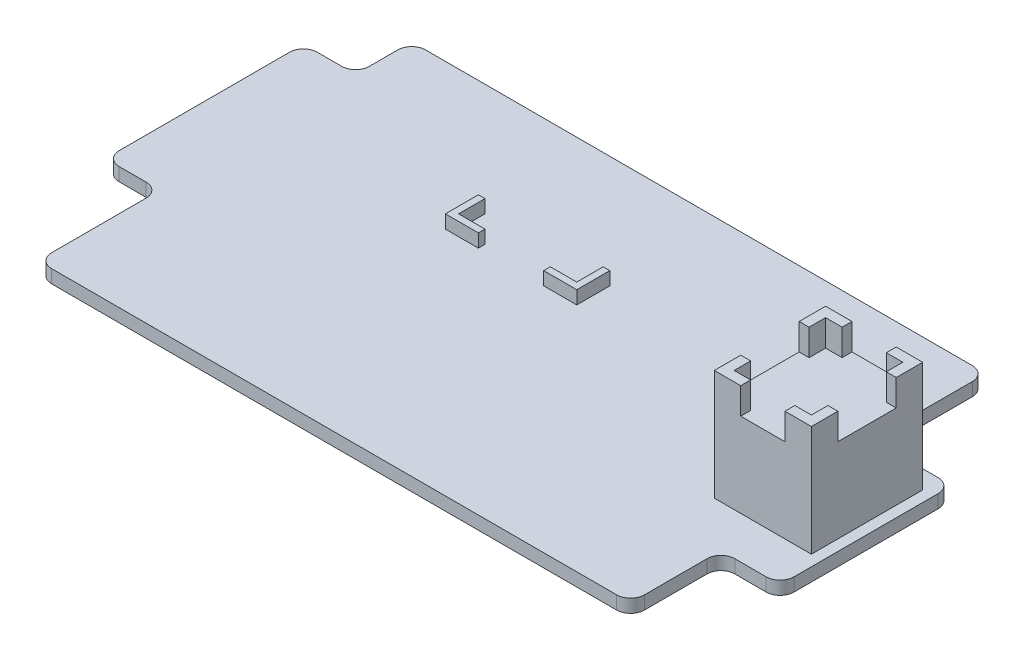
SolidWorks part; units mm, degrees
ref_plane "Front Plane" through (0, 0, 0) normal (0, 0, 1) x (1, 0, 0)
ref_plane "Top Plane" through (0, 0, 0) normal (0, 1, 0) x (1, 0, 0)
ref_plane "Right Plane" through (0, 0, 0) normal (1, 0, 0) x (0, 0, -1)
sketch "Sketch1" plane through (0, 0, 0) normal (0, 1, 0) x (1, 0, 0)
  line L36 (-14.34, 86.924) -> (-97.14, 86.924)
  line L37 (-12.24, 71.7409) -> (-12.24, 84.824)
  line L38 (-2.2334, 69.6409) -> (-10.14, 69.6409)
  line L39 (-0.1334, 45.7095) -> (-0.1334, 67.5409)
  line L40 (-6.9951, 43.6095) -> (-2.2334, 43.6095)
  line L41 (-9.0951, 32.024) -> (-9.0951, 41.5095)
  line L42 (-96.7563, 29.924) -> (-11.1951, 29.924)
  line L43 (-98.8563, 46.3225) -> (-98.8563, 32.024)
  line L44 (-105.0334, 48.4225) -> (-100.9563, 48.4225)
  line L45 (-107.1334, 76.3225) -> (-107.1334, 50.5225)
  line L46 (-101.34, 78.4225) -> (-105.0334, 78.4225)
  line L47 (-99.24, 84.824) -> (-99.24, 80.5225)
  arc A36 (-12.24, 84.824) -> (-14.34, 86.924) centre (-14.34, 84.824) ccw
  arc A37 (-12.24, 71.7409) -> (-10.14, 69.6409) centre (-10.14, 71.7409) ccw
  arc A38 (-0.1334, 67.5409) -> (-2.2334, 69.6409) centre (-2.2334, 67.5409) ccw
  arc A39 (-2.2334, 43.6095) -> (-0.1334, 45.7095) centre (-2.2334, 45.7095) ccw
  arc A40 (-6.9951, 43.6095) -> (-9.0951, 41.5095) centre (-6.9951, 41.5095) ccw
  arc A41 (-11.1951, 29.924) -> (-9.0951, 32.024) centre (-11.1951, 32.024) ccw
  arc A42 (-98.8563, 32.024) -> (-96.7563, 29.924) centre (-96.7563, 32.024) ccw
  arc A43 (-98.8563, 46.3225) -> (-100.9563, 48.4225) centre (-100.9563, 46.3225) ccw
  arc A44 (-107.1334, 50.5225) -> (-105.0334, 48.4225) centre (-105.0334, 50.5225) ccw
  arc A45 (-105.0334, 78.4225) -> (-107.1334, 76.3225) centre (-105.0334, 76.3225) ccw
  arc A46 (-101.34, 78.4225) -> (-99.24, 80.5225) centre (-101.34, 80.5225) ccw
  arc A47 (-97.14, 86.924) -> (-99.24, 84.824) centre (-97.14, 84.824) ccw
extrude "Boss-Extrude1" add sketch "Sketch1" along normal blind 2
sketch "Sketch2" plane through (0, 2, 0) normal (0, 1, 0) x (1, 0, 0)
  line L1 (-52.24, 64.924) -> (-57.24, 64.924)
  line L2 (-52.24, 64.924) -> (-52.24, 69.924)
  line L3 (-52.24, 69.924) -> (-53.24, 69.924)
  line L4 (-57.24, 64.924) -> (-57.24, 65.924)
  line L5 (-72.14, 64.924) -> (-67.14, 64.924)
  line L6 (-72.14, 64.924) -> (-72.14, 69.924)
  line L7 (-72.14, 69.924) -> (-71.14, 69.924)
  line L8 (-67.14, 64.924) -> (-67.14, 65.924)
  line L11 (-67.14, 65.924) -> (-71.14, 65.924)
  line L12 (-71.14, 69.924) -> (-71.14, 65.924)
  line L15 (-57.24, 65.924) -> (-53.24, 65.924)
  line L16 (-53.24, 69.924) -> (-53.24, 65.924)
  line L17 (-57.24, 65.424) -> (-67.14, 65.424) construction
  line L19 (-12.24, 71.7409) -> (-12.24, 84.824) construction
  line L21 (-14.34, 86.924) -> (-97.14, 86.924) construction
  dimension "D1" = 1
  dimension "D2" = 5
  dimension "D3" = 17.9
  dimension "D4" = 21
  dimension "D5" = 41
extrude "Boss-Extrude2" add sketch "Sketch2" along normal blind 2
sketch "Sketch3" plane through (0, 2, 0) normal (0, 1, 0) x (1, 0, 0)
  line L0 (-9.1334, 49.999) -> (-9.1334, 51.499) construction
  line L1 (-1.7834, 49.999) -> (-16.4834, 49.999)
  line L2 (-1.7834, 49.999) -> (-1.7834, 66.849)
  line L3 (-1.7834, 66.849) -> (-16.4834, 66.849)
  line L4 (-16.4834, 49.999) -> (-16.4834, 66.849)
  line L5 (-9.1334, 51.499) -> (-3.2834, 58.424) construction
  line L6 (-3.2834, 58.424) -> (-1.7834, 58.424) construction
  line L7 (-0.1334, 45.7095) -> (-0.1334, 67.5409) construction
  line L8 (-6.9951, 43.6095) -> (-2.2334, 43.6095) construction
  point P6 (-3.2834, 58.424)
  point P9 (-9.1334, 51.499)
  dimension "D1" = 1.5
  dimension "D2" = 14.7
  dimension "D3" = 16.85
  dimension "D4" = 1.65
  dimension "D5" = 6.3895
extrude "Boss-Extrude3" add sketch "Sketch3" along normal blind 12.75
sketch "Sketch4" plane through (0, 14.75, 0) normal (0, 1, 0) x (1, 0, 0)
  line L0 (-1.7834, 49.999) -> (-1.7834, 66.849) construction
  line L1 (-1.7834, 49.999) -> (-5.7834, 49.999)
  line L2 (-1.7834, 49.999) -> (-1.7834, 53.999)
  line L3 (-1.7834, 66.849) -> (-5.7834, 66.849)
  line L4 (-16.4834, 49.999) -> (-16.4834, 53.999)
  line L5 (-16.4834, 49.999) -> (-1.7834, 49.999) construction
  line L6 (-16.4834, 66.849) -> (-16.4834, 49.999) construction
  line L7 (-1.7834, 62.849) -> (-1.7834, 66.849)
  line L8 (-3.2834, 51.499) -> (-5.7834, 51.499)
  line L9 (-3.2834, 51.499) -> (-3.2834, 53.999)
  line L10 (-3.2834, 65.349) -> (-5.7834, 65.349)
  line L11 (-14.9834, 51.499) -> (-14.9834, 53.999)
  line L13 (-5.7834, 49.999) -> (-5.7834, 51.499)
  line L15 (-12.4834, 49.999) -> (-12.4834, 51.499)
  line L16 (-14.9834, 53.999) -> (-16.4834, 53.999)
  line L18 (-14.9834, 62.849) -> (-16.4834, 62.849)
  line L21 (-12.4834, 65.349) -> (-12.4834, 66.849)
  line L23 (-5.7834, 65.349) -> (-5.7834, 66.849)
  line L24 (-3.2834, 62.849) -> (-1.7834, 62.849)
  line L26 (-3.2834, 53.999) -> (-1.7834, 53.999)
  line L28 (-3.2834, 62.849) -> (-3.2834, 65.349)
  line L29 (-14.9834, 62.849) -> (-14.9834, 65.349)
  line L30 (-16.4834, 62.849) -> (-16.4834, 66.849)
  line L31 (-12.4834, 49.999) -> (-16.4834, 49.999)
  line L32 (-12.4834, 51.499) -> (-14.9834, 51.499)
  line L33 (-12.4834, 65.349) -> (-14.9834, 65.349)
  line L34 (-12.4834, 66.849) -> (-16.4834, 66.849)
  point P30 (0, 0)
  dimension "D1" = 1.5
  dimension "D2" = 4
extrude "Boss-Extrude4" add sketch "Sketch4" along normal blind 4
